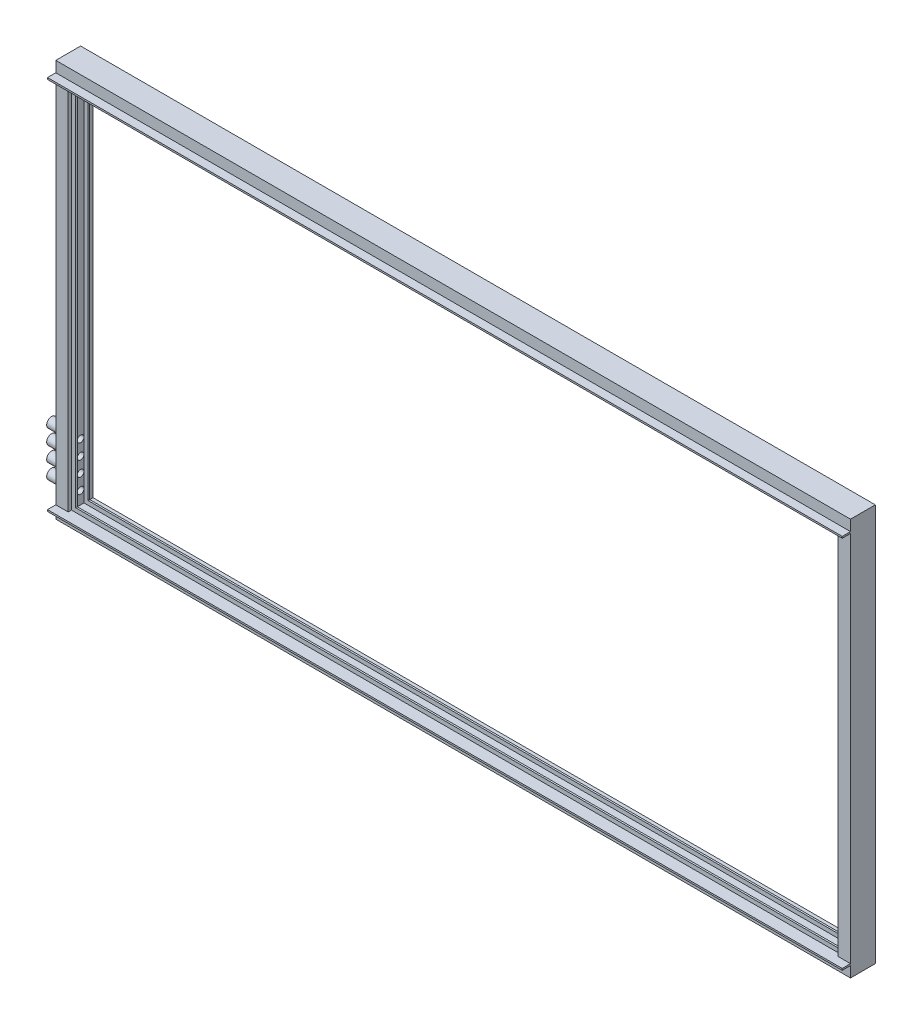
SolidWorks part; units mm, degrees
material "AA356.0-F"
ref_plane "Front Plane" through (0, 0, 0) normal (0, 0, 1) x (1, 0, 0)
ref_plane "Top Plane" through (0, 0, 0) normal (0, 1, 0) x (1, 0, 0)
ref_plane "Right Plane" through (0, 0, 0) normal (1, 0, 0) x (0, 0, -1)
sketch "Sketch2" plane through (0, 0, 0) normal (0, 0, 1) x (1, 0, 0)
  line L1 (609.6, -304.8) -> (-609.6, -304.8)
  line L2 (609.6, -304.8) -> (609.6, 304.8)
  line L3 (609.6, 304.8) -> (-609.6, 304.8)
  line L4 (-609.6, -304.8) -> (-609.6, 304.8)
  line L5 (609.6, -304.8) -> (-609.6, 304.8) construction
  line L6 (609.6, 304.8) -> (-609.6, -304.8) construction
  point P0 (0, 0)
  dimension "D1" = 609.6
  dimension "D2" = 1219.2
sketch "Sketch3" plane through (0, 0, 0) normal (1, 0, 0) x (0, 0, -1)
  line L0 (-19.05, 304.8) -> (19.05, 304.8)
  line L1 (19.05, 304.8) -> (19.05, 285.75)
  line L2 (19.05, 285.75) -> (13.97, 285.75)
  line L3 (12.7, 287.02) -> (12.7, 297.18)
  line L4 (11.43, 298.45) -> (7.62, 298.45)
  line L5 (6.35, 297.18) -> (6.35, 287.02)
  line L6 (5.08, 285.75) -> (-5.08, 285.75)
  line L7 (-6.35, 287.02) -> (-6.35, 297.18)
  line L8 (-7.62, 298.45) -> (-11.43, 298.45)
  line L9 (-12.7, 297.18) -> (-12.7, 287.02)
  line L10 (-13.97, 285.75) -> (-19.05, 285.75)
  line L11 (-19.05, 285.75) -> (-19.05, 304.8)
  line L13 (-12.7, 287.02) -> (-13.97, 285.75)
  line L14 (-5.08, 285.75) -> (-6.35, 287.02)
  line L15 (6.35, 287.02) -> (5.08, 285.75)
  line L16 (13.97, 285.75) -> (12.7, 287.02)
  line L17 (12.7, 297.18) -> (11.43, 298.45)
  line L18 (7.62, 298.45) -> (6.35, 297.18)
  line L19 (-6.35, 297.18) -> (-7.62, 298.45)
  line L20 (-11.43, 298.45) -> (-12.7, 297.18)
  point P4 (12.7, 285.75)
  point P5 (12.7, 298.45)
  point P6 (6.35, 298.45)
  point P7 (6.35, 285.75)
  point P8 (-6.35, 285.75)
  point P9 (-6.35, 298.45)
  point P10 (-12.7, 298.45)
  point P11 (-12.7, 285.75)
  dimension "D1" = 6.35
  dimension "D2" = 12.7
  dimension "D3" = 6.35
  dimension "D4" = 12.7
  dimension "D5" = 6.35
sweep "Sweep1" add profiles "Sketch3" path "Sketch2"
sketch "Sketch4" plane through (-609.6, 0, 0) normal (-1, 0, 0) x (0, 0, 1)
  line L0 (-19.05, -304.8) -> (19.05, -304.8) construction
  circle A0 centre (0, -266.7) radius 5.08
  circle A1 centre (0, -243.84) radius 5.08
  circle A2 centre (0, -220.98) radius 5.08
  circle A3 centre (0, -198.12) radius 5.08
  point P5 (0, -304.8)
  dimension "D1" = 10.16
  dimension "D2" = 38.1
  dimension "D4" = 22.86
  dimension "D3" = 4
extrude "Cut-Extrude4" cut sketch "Sketch4" against normal up to next
sketch "Sketch5" plane through (-609.6, 0, 0) normal (-1, 0, 0) x (0, 0, 1)
  circle A0 centre (0, -198.12) radius 5.08 construction
  circle A1 centre (0, -198.12) radius 5.08
  circle A2 centre (0, -266.7) radius 5.08 construction
  circle A3 centre (0, -243.84) radius 5.08 construction
  circle A4 centre (0, -220.98) radius 5.08 construction
  circle A5 centre (0, -266.7) radius 5.08
  circle A6 centre (0, -243.84) radius 5.08
  circle A7 centre (0, -220.98) radius 5.08
  circle A8 centre (0, -198.12) radius 7.62
  circle A9 centre (0, -220.98) radius 7.62
  circle A10 centre (0, -243.84) radius 7.62
  circle A11 centre (0, -266.7) radius 7.62
  dimension "D1" = 15.24
  dimension "D2" = 15.24
  dimension "D3" = 15.24
  dimension "D4" = 15.24
extrude "Boss-Extrude3" add sketch "Sketch5" along normal blind 25.4
sketch "Sketch7" plane through (0, 0, 19.05) normal (0, 0, 1) x (1, 0, 0)
  line L0 (-609.6, 304.8) -> (-609.6, -304.8) construction
  line L1 (609.6, -304.8) -> (609.6, 304.8) construction
  line L2 (-609.6, 288.29) -> (609.6, 288.29)
  line L3 (-609.6, 288.29) -> (-609.6, 285.75)
  line L4 (-609.6, 285.75) -> (609.6, 285.75)
  line L5 (609.6, 288.29) -> (609.6, 285.75)
  line L6 (590.55, 285.75) -> (-590.55, 285.75) construction
  dimension "D1" = 2.54
extrude "Boss-Extrude4" add sketch "Sketch7" along normal blind 12.7
mirror "Mirror1" about plane through (0, 0, 0) normal (0, 1, 0) of "Boss-Extrude4"
